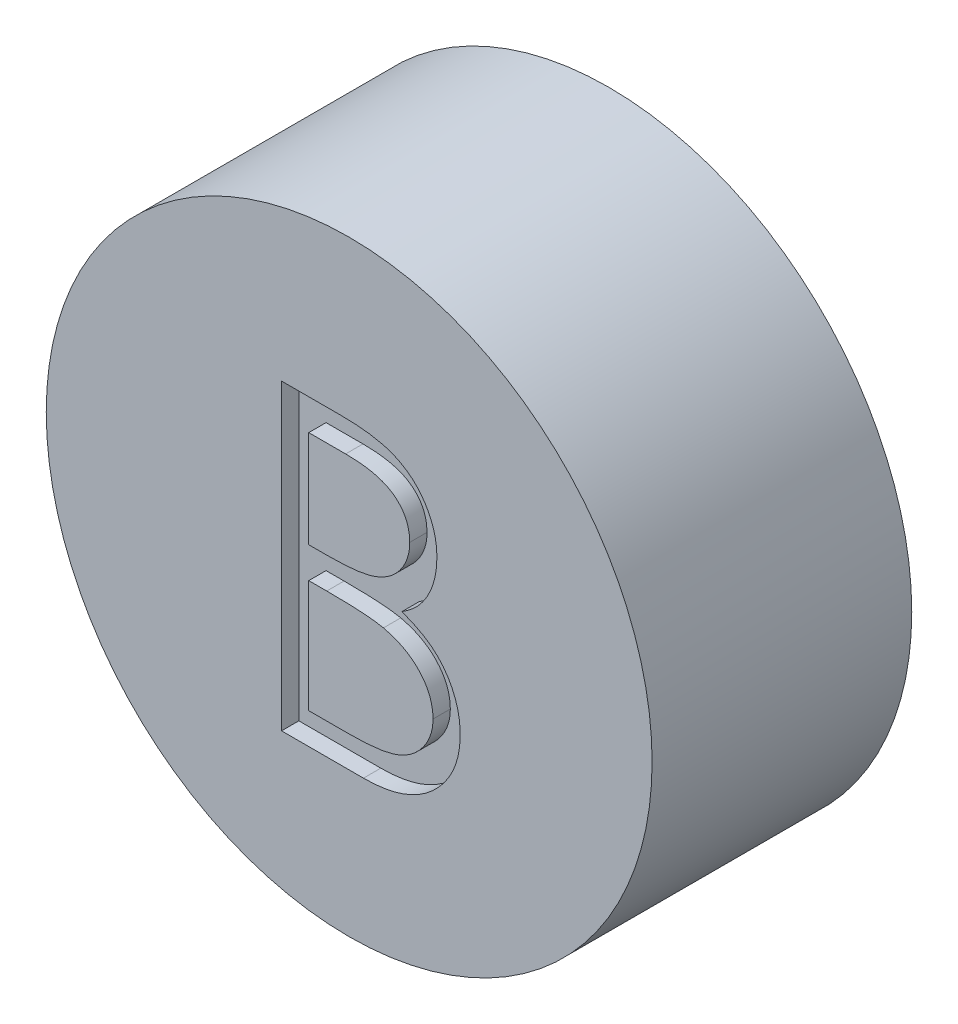
SolidWorks part; units mm, degrees
ref_plane "Front Plane" through (0, 0, 0) normal (0, 0, 1) x (1, 0, 0)
ref_plane "Top Plane" through (0, 0, 0) normal (0, 1, 0) x (1, 0, 0)
ref_plane "Right Plane" through (0, 0, 0) normal (1, 0, 0) x (0, 0, -1)
sketch "Sketch1" plane through (0, 0, 0) normal (0, 0, 1) x (1, 0, 0)
  circle A0 centre (0, 0) radius 3.5
  dimension "D1" = 7
extrude "Boss-Extrude1" add sketch "Sketch1" along normal blind 3
sketch "Sketch2" plane through (0, 0, 3) normal (0, 0, 1) x (1, 0, 0)
  text T0 "B"
extrude "Cut-Extrude1" cut sketch "Sketch2" against normal blind 0.2
